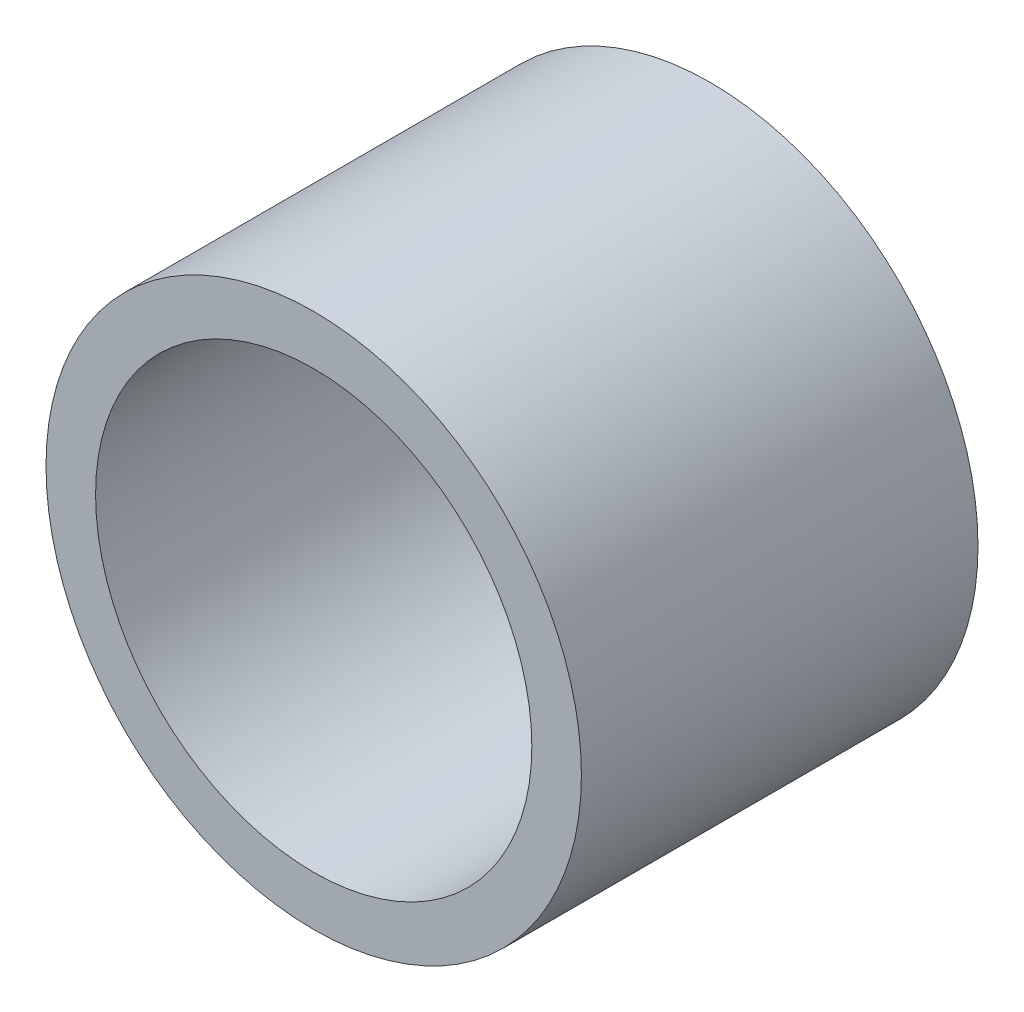
SolidWorks part; units mm, degrees
ref_plane "前基準面" through (0, 0, 0) normal (0, 0, 1) x (1, 0, 0)
ref_plane "上基準面" through (0, 0, 0) normal (0, 1, 0) x (1, 0, 0)
ref_plane "右基準面" through (0, 0, 0) normal (1, 0, 0) x (0, 0, -1)
sketch "草圖1" plane through (0, 0, 0) normal (0, 0, 1) x (1, 0, 0)
  circle A0 centre (0, 0) radius 11
  circle A1 centre (0, 0) radius 13.5
  dimension "D1" = 22
  dimension "D2" = 27
extrude "填料-伸長1" add sketch "草圖1" along normal blind 20
